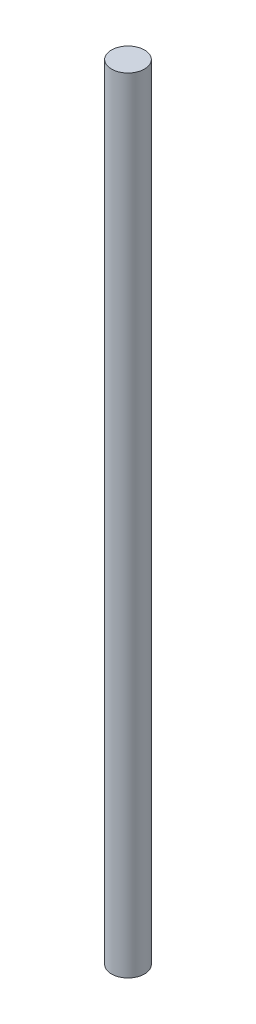
SolidWorks part; units mm, degrees
ref_plane "Front Plane" through (0, 0, 0) normal (0, 0, 1) x (1, 0, 0)
ref_plane "Top Plane" through (0, 0, 0) normal (0, 1, 0) x (1, 0, 0)
ref_plane "Right Plane" through (0, 0, 0) normal (1, 0, 0) x (0, 0, -1)
sketch "Sketch1" plane through (0, 0, 0) normal (0, 1, 0) x (1, 0, 0)
  circle A0 centre (0, 0) radius 1.4732
  dimension "D1" = 2.9464
extrude "Boss-Extrude1" add sketch "Sketch1" along normal blind 69.85
